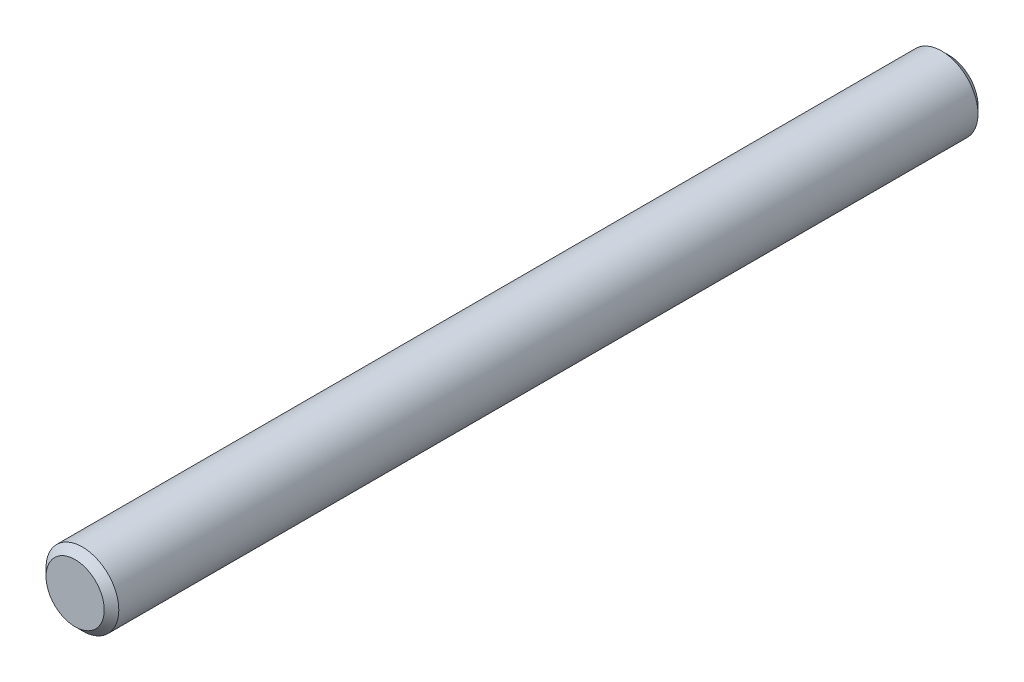
SolidWorks part; units mm, degrees
ref_plane "Front" through (0, 0, 0) normal (0, 0, 1) x (1, 0, 0)
ref_plane "Top" through (0, 0, 0) normal (0, 1, 0) x (1, 0, 0)
ref_plane "Right" through (0, 0, 0) normal (1, 0, 0) x (0, 0, -1)
sketch "Sketch1" plane through (0, 0, 0) normal (0, 0, 1) x (1, 0, 0)
  circle A0 centre (0, 0) radius 2.5
  dimension "D1" = 5
extrude "Boss-Extrude1" add sketch "Sketch1" along normal blind 60
chamfer "Chamfer1" distance 0.5 angle 45 2 edges at (2.5, 0, 0) (2.5, 0, 60)
